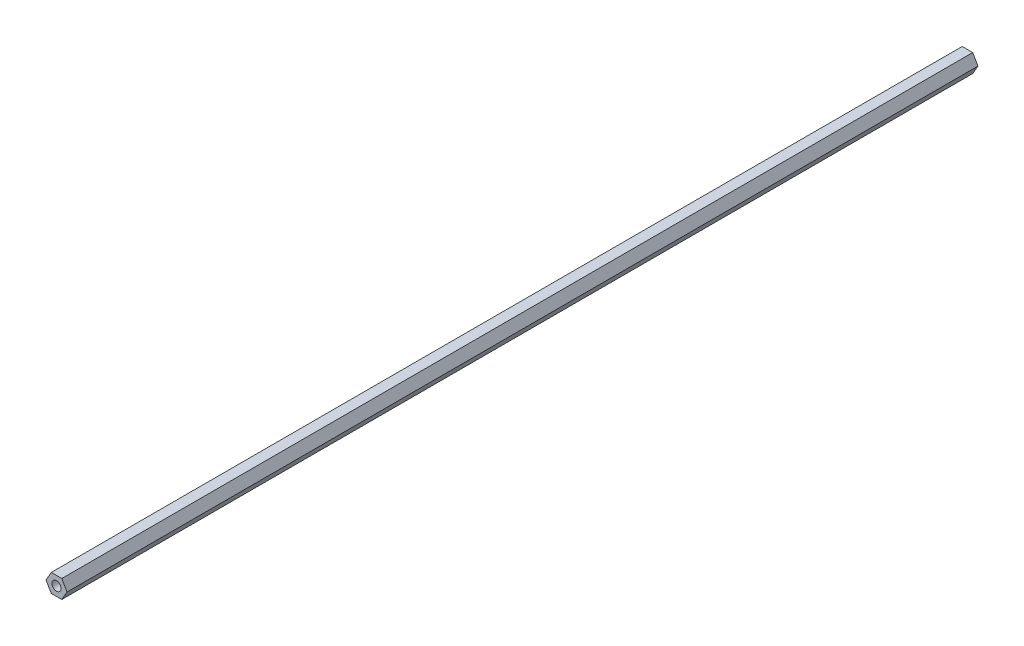
SolidWorks part; units mm, degrees
material "1060 Alloy"
ref_plane "Front Plane" through (0, 0, 0) normal (0, 0, 1) x (1, 0, 0)
ref_plane "Top Plane" through (0, 0, 0) normal (0, 1, 0) x (1, 0, 0)
ref_plane "Right Plane" through (0, 0, 0) normal (1, 0, 0) x (0, 0, -1)
sketch "Sketch1" plane through (0, 0, 0) normal (0, 0, 1) x (1, 0, 0)
  line L1 (-3.6662, 6.35) -> (-7.3323, 0)
  line L2 (-7.3323, 0) -> (-3.6662, -6.35)
  line L3 (-3.6662, -6.35) -> (3.6662, -6.35)
  line L4 (3.6662, -6.35) -> (7.3323, 0)
  line L5 (7.3323, 0) -> (3.6662, 6.35)
  line L6 (3.6662, 6.35) -> (-3.6662, 6.35)
  circle A0 centre (0, 0) radius 6.35 construction
  circle A1 centre (0, 0) radius 3.175
  dimension "D2" = 6.35
  dimension "D1" = 12.7
extrude "Boss-Extrude1" add sketch "Sketch1" along normal blind 635
